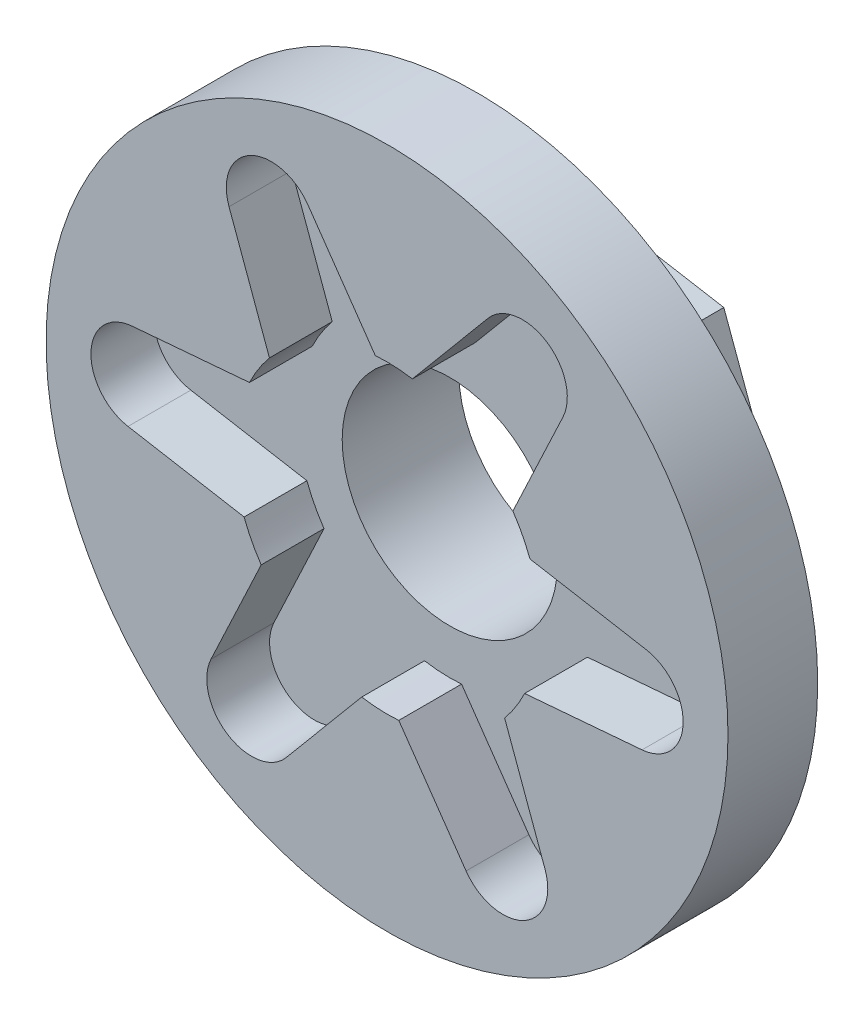
SolidWorks part; units mm, degrees
ref_plane "Front Plane" through (0, 0, 0) normal (0, 0, 1) x (1, 0, 0)
ref_plane "Top Plane" through (0, 0, 0) normal (0, 1, 0) x (1, 0, 0)
ref_plane "Right Plane" through (0, 0, 0) normal (1, 0, 0) x (0, 0, -1)
sketch "Sketch1" plane through (0, 0, 0) normal (0, 0, 1) x (1, 0, 0)
  line L1 (8.7663, 10.5063) -> (-4.7155, 12.845)
  line L2 (-4.7155, 12.845) -> (-13.4819, 2.3387)
  line L3 (-13.4819, 2.3387) -> (-8.7663, -10.5063)
  line L4 (-8.7663, -10.5063) -> (4.7155, -12.845)
  line L5 (4.7155, -12.845) -> (13.4819, -2.3387)
  line L6 (13.4819, -2.3387) -> (8.7663, 10.5063)
  circle A1 centre (0, 0) radius 11.85 construction
  dimension "D4" = 23.7
extrude "Boss-Extrude1" add sketch "Sketch1" along normal blind 5
sketch "Sketch2" plane through (0, 0, 5) normal (0, 0, 1) x (1, 0, 0)
  circle A0 centre (0, 0) radius 19
  dimension "D2" = 38
  dimension "D1" = 0
extrude "Boss-Extrude2" add sketch "Sketch2" along normal blind 5
sketch "Sketch3" plane through (0, 0, 10) normal (0, 0, 1) x (1, 0, 0)
  line L0 (-8.9564, 11.9985) -> (-4.0394, -1.4742)
  line L1 (3.5306, 2.4545) -> (-4.4037, 13.8675)
  line L2 (5.9129, 13.7557) -> (-3.2964, 2.7611)
  line L3 (3.891, -1.8304) -> (9.8078, 10.7474)
  line L4 (14.8692, 1.7572) -> (0.743, 4.2353)
  line L5 (0.3603, -4.2849) -> (14.2114, -3.1201)
  line L6 (8.9564, -11.9985) -> (4.0394, 1.4742)
  line L7 (-3.5306, -2.4545) -> (4.4037, -13.8675)
  line L8 (-5.9129, -13.7557) -> (3.2964, -2.7611)
  line L9 (-3.891, 1.8304) -> (-9.8078, -10.7474)
  line L10 (-14.8692, -1.7572) -> (-0.743, -4.2353)
  line L11 (-0.3603, 4.2849) -> (-14.2114, 3.1201)
  line L12 (0, 0) -> (3.5306, 2.4545) construction
  circle A0 centre (0, 0) radius 4.3
  circle A1 centre (0, 0) radius 19 construction
  circle A2 centre (0, 0) radius 8.5
  circle A3 centre (-6.4564, 12.4405) radius 2.5
  circle A4 centre (7.5456, 11.8116) radius 2.5
  circle A5 centre (14.0019, -0.6289) radius 2.5
  circle A6 centre (6.4564, -12.4405) radius 2.5
  circle A7 centre (-7.5456, -11.8116) radius 2.5
  circle A8 centre (-14.0019, 0.6289) radius 2.5
  point P18 (-4.1235, 12.3009)
  point P19 (-4.1235, 12.3009)
  point P20 (-4.1235, 12.3009)
  point P21 (-4.1235, 12.3009)
  dimension "D1" = 0
  dimension "D2" = 8.6
  dimension "D3" = 0
  dimension "D4" = 5
  dimension "D5" = 2.5
  dimension "D6" = 4.3
  dimension "D7" = 2.5
  dimension "D8" = 13.9
  dimension "D9" = 4.3
  dimension "D10" = 2.5
  dimension "D11" = 4.3
  dimension "D12" = 6
  dimension "D13" = 4.3
  dimension "D14" = 2.5
  dimension "D15" = 4.3
extrude "Cut-Extrude1" cut sketch "Sketch3" against normal blind 3.5
sketch "Sketch4" plane through (0, 0, 0) normal (0, 0, -1) x (-1, 0, 0)
  circle A0 centre (0, 0) radius 6
  circle A1 centre (0, 0) radius 19 construction
  dimension "D1" = 0
  dimension "D2" = 12
extrude "Cut-Extrude2" cut sketch "Sketch4" against normal through all
